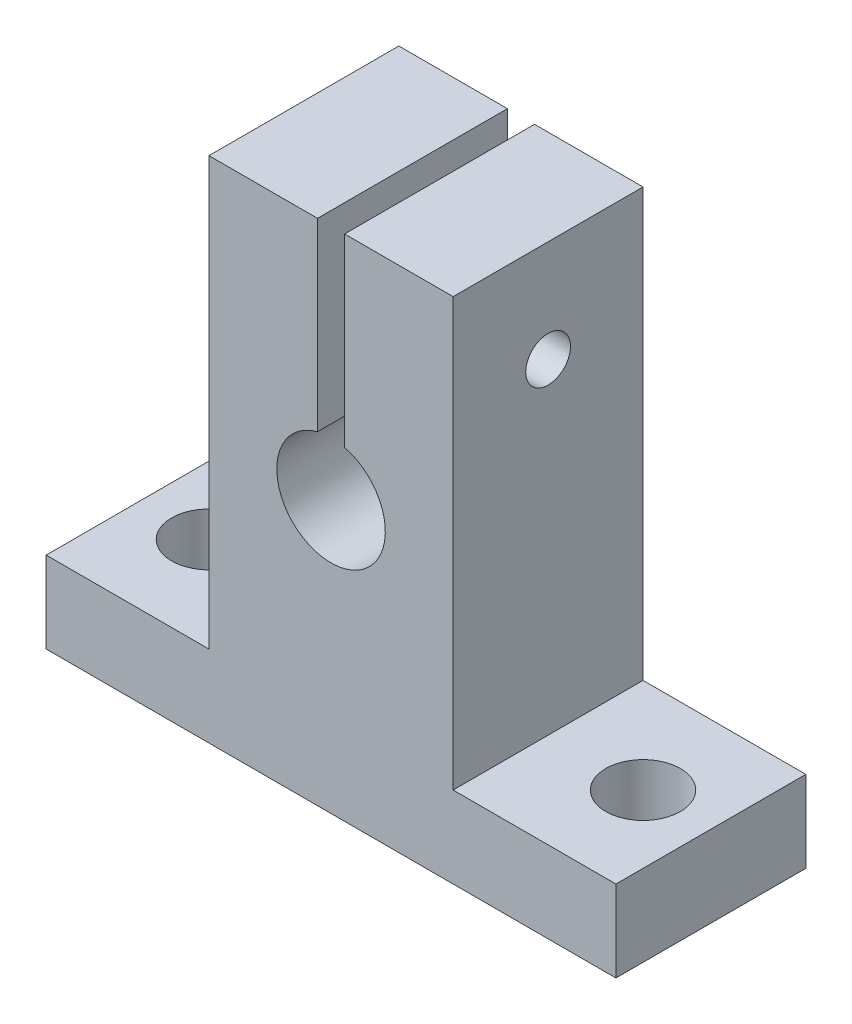
SolidWorks part; units mm, degrees
material "7075-T6, Piastra (SS)"
ref_plane "Płaszczyzna przednia" through (0, 0, 0) normal (0, 0, 1) x (1, 0, 0)
ref_plane "Płaszczyzna górna" through (0, 0, 0) normal (0, 1, 0) x (1, 0, 0)
ref_plane "Płaszczyzna prawa" through (0, 0, 0) normal (1, 0, 0) x (0, 0, -1)
sketch "Sketch2" plane through (0, 0, 0) normal (0, 0, 1) x (1, 0, 0)
  line L0 (-1, 0) -> (-1, 17.5)
  line L1 (-1, 17.5) -> (-9, 17.5)
  line L2 (-9, 17.5) -> (-9, -14)
  line L3 (-9, -14) -> (-21, -14)
  line L4 (-21, -14) -> (-21, -20)
  line L5 (-21, -20) -> (0, -20)
  line L6 (0, -20) -> (0, 0)
  line L7 (0, 0) -> (-1, 0)
  dimension "D1" = 9
  dimension "D2" = 1
  dimension "D3" = 20
  dimension "D4" = 37.5
  dimension "D5" = 6
  dimension "D6" = 21
extrude "Boss-Extrude1" add sketch "Sketch2" along normal blind 14 contours L6 L7 L0 L1 L2 L3 L4 L5
mirror "Mirror1" about plane through (0, -20, 14) normal (-1, 0, 0) of "Boss-Extrude1"
hole_wizard "Tap Drill for M4x0.7 Tap2" positions "Sketch5" profile "Sketch6" hole size "M4x0.7" standard "ANSI Metric" end condition through all
sketch "Sketch5" plane through (-9, 0, 0) normal (-1, 0, 0) x (0, 0, 1)
  line L0 (14, 17.5) -> (0, 17.5) construction
  point P0 (7, 10)
  point P10 (7, 17.5)
  dimension "D1" = 10
sketch "Sketch6" plane through (-9, 10, 7) normal (0, 1, 0) x (0, 0, 1)
  line L0 (0, 0) -> (0, 30)
  line L1 (0, 30) -> (1.65, 30)
  line L2 (1.65, 30) -> (1.65, 0)
  line L5 (1.65, 0) -> (0, 0)
  line L11 (0, -6.35) -> (0, 107.95) construction
  dimension "Thru Hole Dia." = 3.3
  dimension "Thru Hole Depth" = 30
hole_wizard "Ø12.0 (12) Diameter Hole1" positions "Sketch9" profile "Sketch10" hole size "Ø12.0" standard "ANSI Metric" end condition through all
sketch "Sketch9" plane through (0, 0, 0) normal (0, 0, 1) x (1, 0, 0)
  point P0 (0, 0)
sketch "Sketch10" plane through (0, 0, 0) normal (1, 0, 0) x (0, 1, 0)
  line L0 (0, 0) -> (0, 14)
  line L1 (0, 14) -> (4, 14)
  line L2 (4, 14) -> (4, 0)
  line L5 (4, 0) -> (0, 0)
  line L11 (0, -6.35) -> (0, 107.95) construction
  dimension "Thru Hole Dia." = 8
  dimension "Thru Hole Depth" = 14
hole_wizard "Tap Drill for M5x0.8 Tap1" positions "Sketch11" profile "Sketch12" hole size "M5x0.8" standard "ANSI Metric" end condition through all
sketch "Sketch11" plane through (0, -20, 0) normal (0, -1, 0) x (-1, 0, 0)
  line L0 (-16, -7) -> (16, -7) construction
  line L2 (-21, -14) -> (-21, 0) construction
  point P0 (-16, -7)
  point P2 (16, -7)
  point P10 (0, -7)
  point P14 (-21, -7)
  dimension "D1" = 32
sketch "Sketch12" plane through (16, -20, 7) normal (1, 0, 0) x (0, 0, -1)
  line L0 (0, 0) -> (0, 37.5)
  line L1 (0, 37.5) -> (2.75, 37.5)
  line L2 (2.75, 37.5) -> (2.75, 0)
  line L5 (2.75, 0) -> (0, 0)
  line L11 (0, -6.35) -> (0, 107.95) construction
  dimension "Thru Hole Dia." = 5.5
  dimension "Thru Hole Depth" = 37.5
